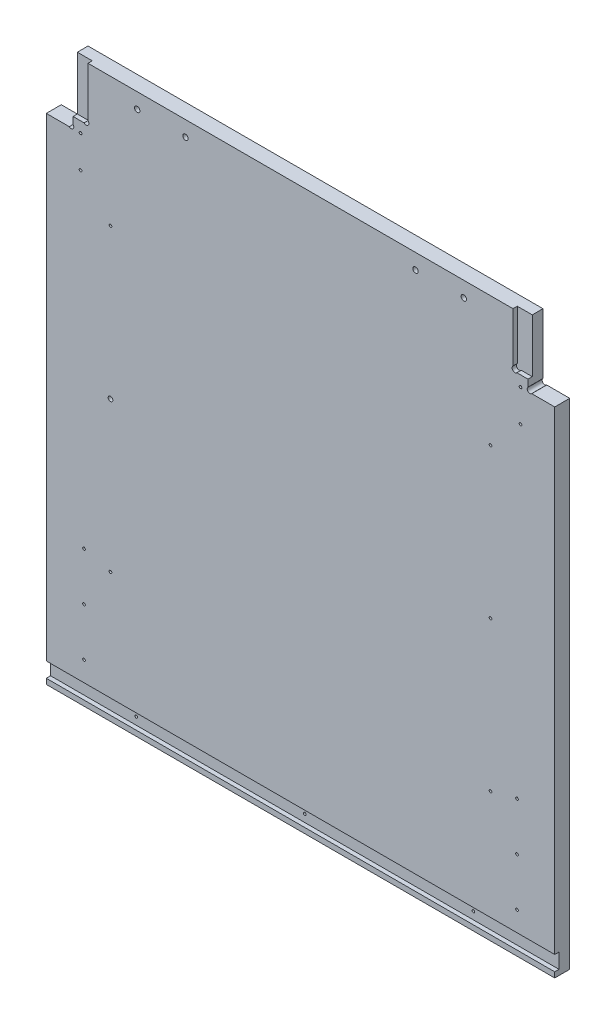
SolidWorks part; units mm, degrees
material "Pine"
ref_plane "Front Plane" through (0, 0, 0) normal (0, 0, 1) x (1, 0, 0)
ref_plane "Top Plane" through (0, 0, 0) normal (0, 1, 0) x (1, 0, 0)
ref_plane "Right Plane" through (0, 0, 0) normal (1, 0, 0) x (0, 0, -1)
sketch "Sketch1" plane through (0, 0, 0) normal (0, 0, 1) x (1, 0, 0)
  line L0 (8932.6508, -5243.5125) -> (10226.1458, -5243.5125)
  line L1 (9086.3208, -4722.0918) -> (10222.9708, -4853.7812)
  line L2 (8914.8708, -6342.0625) -> (10197.5708, -6342.0625)
  line L3 (8914.8708, -5808.6625) -> (10197.5708, -5808.6625)
  line L4 (8919.6333, -5253.0375) -> (10218.2083, -5253.0375)
  line L5 (9134.2633, -4656.1375) -> (9134.2633, -4638.3575)
  line L6 (9091.0833, -4638.3575) -> (9134.2633, -4638.3575)
  line L7 (9091.0833, -4567.2375) -> (9091.0833, -4638.3575)
  line L8 (9134.2633, -4656.1375) -> (9581.3033, -4656.1375)
  line L9 (9091.0833, -4567.2375) -> (9624.4833, -4567.2375)
  line L10 (9581.3033, -4656.1375) -> (9581.3033, -4638.3575)
  line L11 (9581.3033, -4638.3575) -> (9624.4833, -4638.3575)
  line L12 (9624.4833, -4567.2375) -> (9624.4833, -4638.3575)
  line L13 (8932.6508, -5225.7325) -> (9344.9775, -5225.7325)
  line L14 (8932.6508, -5256.2125) -> (8932.6508, -5243.5125)
  line L15 (8911.6958, -5256.2125) -> (8932.6508, -5256.2125)
  line L16 (8914.8708, -4722.0918) -> (9086.3208, -4722.0918)
  line L17 (8911.6958, -4715.5913) -> (8932.6508, -4715.5913)
  line L18 (8914.8708, -6342.0625) -> (8914.8708, -5808.6625)
  line L19 (12082.9917, -4722.0918) -> (10946.3417, -4853.7812)
  line L20 (12236.6617, -5243.5125) -> (10943.1667, -5243.5125)
  line L21 (10951.1042, -5253.0375) -> (12249.6792, -5253.0375)
  line L22 (10838.3917, -5656.2625) -> (11308.2917, -5656.2625)
  line L23 (10838.3917, -5719.7625) -> (11308.2917, -5719.7625)
  line L24 (10838.3917, -5742.5368) -> (11308.2917, -5742.5368)
  line L25 (10806.6417, -6342.0625) -> (11340.0417, -6342.0625)
  line L26 (10803.4667, -6335.7125) -> (11343.2167, -6335.7125)
  line L27 (10803.4667, -6317.9325) -> (11343.2167, -6317.9325)
  line L28 (10943.1667, -5225.7325) -> (11376.4483, -5225.7325)
  line L29 (11506.7292, -4754.5625) -> (10806.6417, -4827.5875)
  line L30 (11506.7292, -4567.2375) -> (11506.7292, -4754.5625)
  line L31 (10806.6417, -4567.2375) -> (10806.6417, -4827.5875)
  line L32 (10806.6417, -4567.2375) -> (11506.7292, -4567.2375)
  line L33 (10235.6708, -6329.3625) -> (10245.1958, -6329.3625)
  line L34 (10245.1958, -6329.3625) -> (10254.7208, -6278.5625)
  line L35 (10302.3458, -6329.3625) -> (10311.8708, -6278.5625)
  line L36 (10302.3458, -6329.3625) -> (10292.8208, -6329.3625)
  line L37 (10245.1958, -5821.3625) -> (10254.7208, -5872.1625)
  line L38 (10235.6708, -5821.3625) -> (10245.1958, -5821.3625)
  line L39 (10292.8208, -5821.3625) -> (10302.3458, -5821.3625)
  line L40 (10302.3458, -5821.3625) -> (10311.8708, -5872.1625)
  line L41 (10235.6708, -5821.3625) -> (10235.6708, -6329.3625)
  line L42 (10254.7208, -5872.1625) -> (10254.7208, -6278.5625)
  line L43 (10311.8708, -5872.1625) -> (10311.8708, -6278.5625)
  line L44 (10292.8208, -5821.3625) -> (10292.8208, -6329.3625)
  line L45 (8932.6508, -5225.7325) -> (8932.6508, -4715.5913)
  line L46 (8911.6958, -4715.5913) -> (8911.6958, -5256.2125)
  line L47 (8914.8708, -5248.275) -> (8914.8708, -4722.0918)
  line L48 (8919.6333, -5253.0375) -> (8914.8708, -5248.275)
  line L49 (8914.8708, -5145.0875) -> (8937.426, -5145.0875)
  line L50 (8914.8708, -5202.2375) -> (8937.426, -5202.2375)
  line L51 (10838.3917, -5656.2625) -> (10838.3917, -5719.7625)
  line L52 (10832.0417, -5736.1868) -> (10856.1717, -5736.1868)
  line L53 (10806.6417, -6342.0625) -> (10806.6417, -5818.7368)
  line L54 (10832.0417, -5649.9125) -> (10856.1717, -5649.9125)
  line L55 (10832.0417, -5726.1125) -> (10856.1717, -5726.1125)
  line L56 (10806.6417, -5818.7368) -> (10833.9015, -5818.7368)
  line L57 (10832.0417, -5806.0442) -> (10851.6815, -5806.0442)
  line L58 (10856.1717, -5801.5541) -> (10856.1717, -5736.1868)
  line L59 (10838.3917, -5814.2467) -> (10838.3917, -5742.5368)
  line L60 (10832.0417, -5806.0442) -> (10832.0417, -5736.1868)
  line L61 (10803.4667, -6317.9325) -> (10803.4667, -6335.7125)
  line L62 (10197.5708, -5808.6625) -> (10197.5708, -6342.0625)
  line L63 (9762.3842, -6348.4125) -> (9762.3842, -5802.3125)
  line L64 (9780.1642, -6348.4125) -> (9762.3842, -6348.4125)
  line L65 (9780.1642, -5802.3125) -> (9780.1642, -6348.4125)
  line L66 (9762.3842, -5802.3125) -> (9780.1642, -5802.3125)
  line L67 (9332.2775, -6348.4125) -> (9332.2775, -5802.3125)
  line L68 (9332.2775, -6348.4125) -> (9350.0575, -6348.4125)
  line L69 (9350.0575, -5802.3125) -> (9350.0575, -6348.4125)
  line L70 (9332.2775, -5802.3125) -> (9350.0575, -5802.3125)
  line L71 (9993.8374, -6061.075) -> (9993.8374, -6045.2418)
  line L72 (9998.5999, -6065.8375) -> (10014.4331, -6065.8375)
  line L73 (9998.5999, -6084.8875) -> (10014.4331, -6084.8875)
  line L74 (9993.8374, -6105.4832) -> (9993.8374, -6089.65)
  line L75 (9974.7874, -6105.4832) -> (9974.7874, -6089.65)
  line L76 (9954.1917, -6084.8875) -> (9970.0249, -6084.8875)
  line L77 (9974.7874, -6061.075) -> (9974.7874, -6045.2418)
  line L78 (9954.1917, -6065.8375) -> (9970.0249, -6065.8375)
  line L79 (10793.9417, -6237.2875) -> (10816.4969, -6237.2875)
  line L80 (10793.9417, -6294.4375) -> (10816.4969, -6294.4375)
  line L81 (10856.1717, -5649.9125) -> (10856.1717, -5726.1125)
  line L82 (10832.0417, -5726.1125) -> (10832.0417, -5649.9125)
  line L83 (10226.1458, -5225.7325) -> (10226.1458, -5243.5125)
  line L84 (10205.1908, -5257.8) -> (10205.1908, -4844.2499)
  line L85 (10230.9083, -4844.2499) -> (10230.9083, -5257.8)
  line L86 (10205.1908, -5257.8) -> (10230.9083, -5257.8)
  line L87 (10205.1908, -4844.2499) -> (10230.9083, -4844.2499)
  line L88 (10946.3417, -5176.8375) -> (10968.8969, -5176.8375)
  line L89 (9349.4676, -5141.9125) -> (9358.2674, -5141.9125)
  line L90 (10946.3417, -5119.6875) -> (10968.8969, -5119.6875)
  line L91 (9929.011, -4660.9635) -> (10066.0807, -4660.9635)
  line L92 (9929.011, -4678.7435) -> (10066.0807, -4678.7435)
  line L93 (10943.1667, -5225.7325) -> (10943.1667, -5243.5125)
  line L94 (10946.3417, -5248.275) -> (10951.1042, -5253.0375)
  line L95 (10946.3417, -5257.8063) -> (10946.3417, -4849.0188)
  line L96 (10964.1217, -5257.8) -> (10964.1217, -4844.2499)
  line L97 (10938.4042, -4844.2499) -> (10938.4042, -5257.8)
  line L98 (10938.4042, -5257.8) -> (10964.1217, -5257.8)
  line L99 (10964.1217, -4844.2499) -> (10938.4042, -4844.2499)
  line L100 (10344.8908, -4560.8875) -> (10369.0208, -4560.8875)
  line L101 (10344.8908, -4560.8875) -> (10369.0208, -4560.8875)
  line L102 (10800.2917, -4560.8875) -> (10824.4217, -4560.8875)
  line L103 (10200.4156, -5119.6875) -> (10222.9708, -5119.6875)
  line L104 (10200.4156, -5176.8375) -> (10222.9708, -5176.8375)
  line L105 (9344.9775, -5146.4026) -> (9344.9775, -5225.7325)
  line L106 (10344.8908, -4560.8875) -> (10344.8908, -4833.9375)
  line L107 (9792.8642, -5225.7325) -> (9792.8642, -5146.4026)
  line L108 (9362.7575, -5225.7325) -> (9775.0842, -5225.7325)
  line L109 (9680.3633, -4761.8396) -> (9680.3633, -4559.9604)
  line L110 (9656.2333, -4559.9604) -> (9680.3633, -4559.9604)
  line L111 (9656.2333, -4761.8396) -> (9680.3633, -4761.8396)
  line L112 (9656.2333, -4761.8396) -> (9656.2333, -4559.9604)
  line L113 (9779.5743, -5141.9125) -> (9788.374, -5141.9125)
  line L114 (10070.5708, -4665.4536) -> (10070.5708, -4674.2534)
  line L115 (9924.5208, -4674.2534) -> (9924.5208, -4665.4536)
  line L116 (12127.4417, -6188.3925) -> (12205.5015, -6188.3925)
  line L117 (12209.9917, -6170.6125) -> (12209.9917, -6183.9024)
  line L118 (9792.8642, -5225.7325) -> (10226.1458, -5225.7325)
  line L119 (9662.5833, -4754.5625) -> (10362.6708, -4827.5875)
  line L120 (9662.5833, -4567.2375) -> (9662.5833, -4754.5625)
  line L121 (10362.6708, -4567.2375) -> (10362.6708, -4827.5875)
  line L122 (9662.5833, -4567.2375) -> (10362.6708, -4567.2375)
  line L123 (10824.4217, -4833.9375) -> (10800.2917, -4833.9375)
  line L124 (10800.2917, -4833.9375) -> (10800.2917, -4560.8875)
  line L125 (10824.4217, -4560.8875) -> (10824.4217, -4833.9375)
  line L126 (10344.8908, -4833.9375) -> (10369.0208, -4833.9375)
  line L127 (10369.0208, -4833.9375) -> (10369.0208, -4560.8875)
  line L128 (10222.9708, -5248.275) -> (10218.2083, -5253.0375)
  line L129 (10222.9708, -5257.8063) -> (10222.9708, -4849.0188)
  line L130 (11734.6544, -5701.375) -> (11739.2301, -5701.375)
  line L131 (9362.7575, -5225.7325) -> (9362.7575, -5146.4026)
  line L132 (9775.0842, -5146.4026) -> (9775.0842, -5225.7325)
  line L133 (11761.3864, -5701.375) -> (11756.8282, -5701.375)
  line L134 (11734.6544, -5693.755) -> (11739.2301, -5693.755)
  line L135 (11761.4039, -5693.755) -> (11756.8282, -5693.755)
  line L136 (11734.6544, -5701.375) -> (11739.2301, -5701.375)
  line L137 (11744.3462, -5721.3024) -> (11744.3462, -5706.4179)
  line L138 (11751.7122, -5721.3024) -> (11751.7122, -5706.4179)
  line L139 (11740.0917, -6170.6125) -> (11740.0917, -6183.9024)
  line L140 (11689.2917, -6188.3925) -> (11822.6417, -6188.3925)
  line L141 (11689.2917, -6348.4093) -> (11689.2917, -6164.2657)
  line L142 (11689.2917, -6164.2657) -> (11746.4417, -6164.2657)
  line L143 (11746.4417, -6164.2657) -> (11746.4417, -6188.3925)
  line L144 (11689.2917, -6164.2657) -> (11746.4417, -6164.2657)
  line L145 (11340.0417, -5818.7368) -> (11340.0417, -6342.0625)
  line L146 (11290.5117, -5726.1125) -> (11314.6417, -5726.1125)
  line L147 (11290.5117, -5649.9125) -> (11290.5117, -5726.1125)
  line L148 (11340.0417, -5818.7368) -> (11312.7818, -5818.7368)
  line L149 (11314.6417, -5806.0442) -> (11295.0018, -5806.0442)
  line L150 (11290.5117, -5801.5541) -> (11290.5117, -5736.1868)
  line L151 (11308.2917, -5814.2467) -> (11308.2917, -5742.5368)
  line L152 (11314.6417, -5806.0442) -> (11314.6417, -5736.1868)
  line L153 (11290.5117, -5736.1868) -> (11314.6417, -5736.1868)
  line L154 (11848.0417, -6267.1325) -> (11962.3417, -6267.1325)
  line L155 (11962.3417, -6267.1325) -> (11962.3417, -6203.6325)
  line L156 (11343.2167, -6317.9325) -> (11343.2167, -6335.7125)
  line L157 (11365.4417, -5656.2625) -> (11365.4417, -5719.7625)
  line L158 (11365.4417, -5656.2625) -> (11479.7417, -5656.2625)
  line L159 (11778.1917, -6071.3937) -> (11802.3217, -6071.3937)
  line L160 (11314.6417, -5726.1125) -> (11314.6417, -5649.9125)
  line L161 (11314.6417, -5649.9125) -> (11290.5117, -5649.9125)
  line L162 (11308.2917, -5719.7625) -> (11308.2917, -5656.2625)
  line L163 (11689.2917, -6348.4093) -> (11713.4217, -6348.4093)
  line L164 (12203.6417, -6164.2657) -> (12260.7917, -6164.2657)
  line L165 (11713.4217, -6348.4093) -> (11713.4217, -6164.2657)
  line L166 (11695.6417, -6342.0625) -> (11695.6417, -6170.6125)
  line L167 (11695.6417, -6048.5337) -> (11699.4517, -6052.3437)
  line L168 (11822.6417, -6292.5325) -> (11822.6417, -6188.3925)
  line L169 (11695.6417, -6342.0625) -> (11695.6417, -6170.6125)
  line L170 (11848.0417, -6203.6325) -> (11962.3417, -6203.6325)
  line L171 (11848.0417, -6203.6325) -> (11848.0417, -6267.1325)
  line L172 (11987.7417, -6267.1325) -> (11987.7417, -6203.6325)
  line L173 (11784.5417, -6077.7437) -> (11784.5417, -6141.2438)
  line L174 (11517.8417, -5656.2625) -> (11632.1417, -5656.2625)
  line L175 (11632.1417, -5656.2625) -> (11632.1417, -5719.7625)
  line L176 (11632.1417, -5719.7625) -> (11517.8417, -5719.7625)
  line L177 (11517.8417, -5719.7625) -> (11517.8417, -5656.2625)
  line L178 (11692.4667, -6028.2137) -> (11692.4667, -6045.9937)
  line L179 (11695.6417, -5979.3188) -> (11718.1969, -5979.3188)
  line L180 (11695.6417, -5922.1687) -> (11718.1969, -5922.1687)
  line L181 (11821.0415, -5722.9375) -> (11821.0415, -5943.6)
  line L182 (11687.7042, -5651.5) -> (11701.9917, -5651.5)
  line L183 (11687.7042, -5651.5) -> (11687.7042, -6055.5251)
  line L184 (11687.7042, -6055.5251) -> (11701.9917, -6055.5251)
  line L185 (11701.9917, -6055.5251) -> (11701.9917, -5651.5)
  line L186 (11695.6417, -6055.2013) -> (11695.6417, -5649.595)
  line L187 (11695.6417, -5656.2625) -> (11695.6417, -6048.5337)
  line L188 (11695.6417, -6170.6125) -> (11740.0917, -6170.6125)
  line L189 (12203.6417, -6164.2657) -> (12203.6417, -6188.3925)
  line L190 (12254.4417, -6342.0625) -> (12254.4417, -6170.6125)
  line L191 (12129.0419, -5943.6) -> (12129.0419, -5722.9375)
  line L192 (12254.4417, -6048.5337) -> (12250.6317, -6052.3437)
  line L193 (12257.6167, -6045.9937) -> (12257.6167, -6028.2137)
  line L194 (12248.0917, -5651.5) -> (12262.3792, -5651.5)
  line L195 (12262.3792, -5651.5) -> (12262.3792, -6055.5251)
  line L196 (12262.3792, -6055.5251) -> (12248.0917, -6055.5251)
  line L197 (12248.0917, -6055.5251) -> (12248.0917, -5651.5)
  line L198 (12254.4417, -6141.2438) -> (12254.4417, -6077.7437)
  line L199 (12236.6617, -6164.2657) -> (12260.7917, -6164.2657)
  line L200 (12102.0417, -6267.1325) -> (11987.7417, -6267.1325)
  line L201 (11330.1865, -6237.2875) -> (11352.7417, -6237.2875)
  line L202 (11330.1865, -6294.4375) -> (11352.7417, -6294.4375)
  line L203 (11474.6617, -5851.8425) -> (11492.4417, -5851.8425)
  line L204 (11474.6617, -5808.6625) -> (11474.6617, -5851.8425)
  line L205 (11403.5417, -5808.6625) -> (11474.6617, -5808.6625)
  line L206 (11492.4417, -5851.8425) -> (11492.4417, -6298.8825)
  line L207 (11403.5417, -6342.0625) -> (11403.5417, -5808.6625)
  line L208 (11474.6617, -6298.8825) -> (11492.4417, -6298.8825)
  line L209 (11474.6617, -6342.0625) -> (11474.6617, -6298.8825)
  line L210 (11403.5417, -6342.0625) -> (11474.6617, -6342.0625)
  line L211 (11619.4417, -5851.8425) -> (11601.6617, -5851.8425)
  line L212 (11601.6617, -5808.6625) -> (11601.6617, -5851.8425)
  line L213 (11530.5417, -5808.6625) -> (11601.6617, -5808.6625)
  line L214 (11619.4417, -5851.8425) -> (11619.4417, -6298.8825)
  line L215 (11530.5417, -6342.0625) -> (11530.5417, -5808.6625)
  line L216 (11619.4417, -6298.8825) -> (11601.6617, -6298.8825)
  line L217 (11601.6617, -6342.0625) -> (11601.6617, -6298.8825)
  line L218 (11530.5417, -6342.0625) -> (11601.6617, -6342.0625)
  line L219 (11479.7417, -5719.7625) -> (11479.7417, -5656.2625)
  line L220 (11365.4417, -5719.7625) -> (11479.7417, -5719.7625)
  line L221 (11778.1917, -6147.5937) -> (11802.3217, -6147.5937)
  line L222 (11802.3217, -6071.3937) -> (11802.3217, -6147.5937)
  line L223 (11778.1917, -6147.5937) -> (11778.1917, -6071.3937)
  line L224 (12254.4417, -5922.1687) -> (12231.8865, -5922.1687)
  line L225 (12254.4417, -5979.3188) -> (12231.8865, -5979.3188)
  line L226 (12254.4417, -6055.2013) -> (12254.4417, -5649.595)
  line L227 (12254.4417, -6048.5337) -> (12254.4417, -5656.2625)
  line L228 (11841.6917, -5702.2873) -> (12108.3917, -5702.2873)
  line L229 (11822.6417, -6292.5325) -> (12127.4417, -6292.5325)
  line L230 (12127.4417, -6292.5325) -> (12127.4417, -6188.3925)
  line L231 (12254.4417, -6170.6125) -> (12209.9917, -6170.6125)
  line L232 (11695.6417, -6342.0625) -> (12254.4417, -6342.0625)
  line L233 (12236.6617, -6348.4093) -> (12260.7917, -6348.4093)
  line L234 (12260.7917, -6348.4093) -> (12260.7917, -6164.2657)
  line L235 (12236.6617, -6348.4093) -> (12236.6617, -6164.2657)
  line L236 (12102.0417, -6203.6325) -> (12102.0417, -6267.1325)
  line L237 (11987.7417, -6203.6325) -> (12102.0417, -6203.6325)
  line L238 (12236.6617, -6147.5937) -> (12236.6617, -6071.3937)
  line L239 (12203.6417, -6188.3925) -> (12260.7917, -6188.3925)
  line L240 (11098.7417, -4665.4536) -> (11098.7417, -4674.2534)
  line L241 (11394.2283, -5146.4026) -> (11394.2283, -5225.7325)
  line L242 (11376.4483, -5225.7325) -> (11376.4483, -5146.4026)
  line L243 (11394.2283, -5225.7325) -> (11806.555, -5225.7325)
  line L244 (11841.6917, -5964.2502) -> (12108.3917, -5964.2502)
  line L245 (12236.6617, -6147.5937) -> (12260.7917, -6147.5937)
  line L246 (12236.6617, -5256.2125) -> (12236.6617, -5243.5125)
  line L247 (12260.7917, -6147.5937) -> (12260.7917, -6071.3937)
  line L248 (12260.7917, -6071.3937) -> (12236.6617, -6071.3937)
  line L249 (12254.4417, -6077.7437) -> (11784.5417, -6077.7437)
  line L250 (11784.5417, -6141.2438) -> (12254.4417, -6141.2438)
  line L252 (12254.4417, -5656.2625) -> (11695.6417, -5656.2625)
  line L253 (11699.4517, -6052.3437) -> (12250.6317, -6052.3437)
  line L254 (11692.4667, -6045.9937) -> (12257.6167, -6045.9937)
  line L255 (11692.4667, -6028.2137) -> (12257.6167, -6028.2137)
  line L256 (11824.335, -5146.4026) -> (11824.335, -5225.7325)
  line L257 (11811.0451, -5141.9125) -> (11819.8449, -5141.9125)
  line L258 (11244.7917, -4674.2534) -> (11244.7917, -4665.4536)
  line L259 (11806.555, -5225.7325) -> (11806.555, -5146.4026)
  line L260 (11488.9492, -4761.8396) -> (11488.9492, -4559.9604)
  line L261 (11488.9492, -4559.9604) -> (11513.0792, -4559.9604)
  line L262 (11488.9492, -4761.8396) -> (11513.0792, -4761.8396)
  line L263 (11513.0792, -4761.8396) -> (11513.0792, -4559.9604)
  line L264 (11240.3015, -4660.9635) -> (11103.2318, -4660.9635)
  line L265 (11103.2318, -4678.7435) -> (11240.3015, -4678.7435)
  line L266 (12236.6617, -5225.7325) -> (12236.6617, -4715.5913)
  line L267 (12257.6167, -4715.5913) -> (12257.6167, -5256.2125)
  line L268 (12254.4417, -5248.275) -> (12254.4417, -4722.0918)
  line L269 (12236.6617, -5225.7325) -> (11824.335, -5225.7325)
  line L270 (12035.0492, -4656.1375) -> (12035.0492, -4638.3575)
  line L271 (12078.2292, -4638.3575) -> (12035.0492, -4638.3575)
  line L272 (12078.2292, -4567.2375) -> (12078.2292, -4638.3575)
  line L273 (12035.0492, -4656.1375) -> (11588.0092, -4656.1375)
  line L274 (11544.8292, -4567.2375) -> (12078.2292, -4567.2375)
  line L275 (11588.0092, -4656.1375) -> (11588.0092, -4638.3575)
  line L276 (11544.8292, -4638.3575) -> (11588.0092, -4638.3575)
  line L277 (11544.8292, -4567.2375) -> (11544.8292, -4638.3575)
  line L278 (12249.6792, -5253.0375) -> (12254.4417, -5248.275)
  line L280 (12257.6167, -5256.2125) -> (12236.6617, -5256.2125)
  line L281 (12231.8865, -5145.0875) -> (12254.4417, -5145.0875)
  line L282 (12231.8865, -5202.2375) -> (12254.4417, -5202.2375)
  line L283 (12236.6617, -4715.5913) -> (12257.6167, -4715.5913)
  line L284 (12082.9917, -4722.0918) -> (12254.4417, -4722.0918)
  line L285 (11380.9385, -5141.9125) -> (11389.7382, -5141.9125)
  circle A0 centre (8923.7608, -4778.9042) radius 1.5875
  circle A1 centre (9062.6598, -4736.3765) radius 2.3685
  circle A2 centre (9051.3958, -6281.7375) radius 22.225
  circle A3 centre (9083.1458, -6249.9875) radius 1.5875
  circle A4 centre (9083.1458, -6313.4875) radius 1.5875
  circle A5 centre (9019.6458, -6249.9875) radius 1.5875
  circle A6 centre (9019.6458, -6313.4875) radius 1.5875
  circle A7 centre (8972.3383, -5202.2375) radius 1.5875
  circle A8 centre (8923.7608, -5015.9708) radius 1.5875
  circle A9 centre (8923.7608, -5134.5042) radius 1.5875
  circle A10 centre (9054.5708, -5234.6225) radius 1.5875
  circle A11 centre (8923.7608, -4897.4375) radius 1.5875
  circle A12 centre (8972.3383, -5087.9375) radius 1.5875
  circle A13 centre (8972.3383, -5145.0875) radius 1.5875
  circle A14 centre (10847.2817, -5668.9625) radius 1.5875
  circle A15 centre (10847.2817, -5707.0625) radius 1.5875
  circle A16 centre (10847.2817, -5755.2368) radius 1.5875
  circle A17 centre (10851.4092, -6237.2875) radius 1.5875
  circle A18 centre (10851.4092, -6294.4375) radius 1.5875
  circle A19 centre (10847.2817, -5793.3442) radius 1.5875
  arc A20 (10833.9015, -5818.7368) -> (10838.3917, -5814.2467) centre (10836.1466, -5816.4918) ccw
  arc A21 (10851.6815, -5806.0442) -> (10856.1717, -5801.5541) centre (10853.9266, -5803.7992) ccw
  circle A22 centre (10882.8417, -6040.4375) radius 1.5875
  circle A23 centre (10882.8417, -6218.2375) radius 1.5875
  circle A24 centre (10882.8417, -5862.6375) radius 1.5875
  circle A25 centre (10908.2417, -6326.8225) radius 1.5875
  circle A26 centre (10908.2417, -6326.8225) radius 1.5875
  circle A27 centre (10851.4092, -6180.1375) radius 1.5875
  circle A28 centre (10815.5317, -4783.4231) radius 1.5875
  circle A29 centre (10815.5317, -4696.9488) radius 1.5875
  circle A30 centre (10815.5317, -4610.4746) radius 1.5875
  circle A31 centre (10979.1323, -4867.0082) radius 2.3685
  circle A32 centre (10190.1802, -4867.0082) radius 2.3685
  circle A33 centre (10955.2317, -4929.9812) radius 1.5875
  circle A34 centre (10955.2317, -5031.5812) radius 1.5875
  circle A35 centre (10214.0808, -4929.9812) radius 1.5875
  circle A36 centre (10214.0808, -5031.5812) radius 1.5875
  circle A37 centre (9341.1675, -6265.8625) radius 1.5875
  circle A38 centre (9771.2742, -5884.8625) radius 1.5875
  circle A39 centre (9771.2742, -6138.8625) radius 1.5875
  circle A40 centre (9771.2742, -6011.8625) radius 1.5875
  arc A41 (10036.2287, -6113.8083) -> (10051.3426, -6111.6033) centre (10042.9639, -6107.0732) ccw
  arc A42 (10051.3426, -6111.6033) -> (10051.3426, -6039.1217) centre (9984.3124, -6075.3625) ccw
  arc A43 (10051.3426, -6039.1217) -> (10036.2287, -6036.9167) centre (10042.9639, -6043.6518) ccw
  arc A44 (10034.5851, -6102.5431) -> (10034.5851, -6048.1819) centre (9984.3124, -6075.3625) ccw
  arc A45 (10034.5851, -6102.5431) -> (10036.2287, -6113.8083) centre (10042.9639, -6107.0732) ccw
  arc A46 (10036.2287, -6036.9167) -> (10034.5851, -6048.1819) centre (10042.9639, -6043.6518) ccw
  arc A47 (9945.8666, -6127.2787) -> (9948.0717, -6142.3927) centre (9952.6018, -6134.0139) ccw
  arc A48 (9948.0717, -6142.3927) -> (10020.5532, -6142.3927) centre (9984.3124, -6075.3625) ccw
  arc A49 (10020.5532, -6142.3927) -> (10022.7583, -6127.2787) centre (10016.0231, -6134.0139) ccw
  arc A50 (9957.1319, -6125.6352) -> (10011.493, -6125.6352) centre (9984.3124, -6075.3625) ccw
  arc A51 (9957.1319, -6125.6352) -> (9945.8666, -6127.2787) centre (9952.6018, -6134.0139) ccw
  arc A52 (10022.7583, -6127.2787) -> (10011.493, -6125.6352) centre (10016.0231, -6134.0139) ccw
  arc A53 (9932.3962, -6036.9167) -> (9917.2822, -6039.1217) centre (9925.661, -6043.6518) ccw
  arc A54 (9917.2822, -6039.1217) -> (9917.2822, -6111.6033) centre (9984.3124, -6075.3625) ccw
  arc A55 (9917.2822, -6111.6033) -> (9932.3962, -6113.8083) centre (9925.661, -6107.0732) ccw
  arc A56 (9934.0398, -6048.1819) -> (9934.0398, -6102.5431) centre (9984.3124, -6075.3625) ccw
  arc A57 (9934.0398, -6048.1819) -> (9932.3962, -6036.9167) centre (9925.661, -6043.6518) ccw
  arc A58 (9932.3962, -6113.8083) -> (9934.0398, -6102.5431) centre (9925.661, -6107.0732) ccw
  arc A59 (9945.8666, -6023.4463) -> (9957.1319, -6025.0898) centre (9952.6018, -6016.7111) ccw
  arc A60 (10011.493, -6025.0898) -> (10022.7583, -6023.4463) centre (10016.0231, -6016.7111) ccw
  arc A61 (10011.493, -6025.0898) -> (9957.1319, -6025.0898) centre (9984.3124, -6075.3625) ccw
  arc A62 (9948.0717, -6008.3323) -> (9945.8666, -6023.4463) centre (9952.6018, -6016.7111) ccw
  arc A63 (10020.5532, -6008.3323) -> (9948.0717, -6008.3323) centre (9984.3124, -6075.3625) ccw
  arc A64 (10022.7583, -6023.4463) -> (10020.5532, -6008.3323) centre (10016.0231, -6016.7111) ccw
  arc A65 (10005.0943, -6187.7574) -> (10096.7073, -6096.1443) centre (9984.3124, -6075.3625) ccw
  arc A66 (9993.8374, -6178.3911) -> (10005.0943, -6187.7574) centre (10003.3624, -6178.3911) ccw
  arc A67 (10001.6306, -6169.0249) -> (10077.9748, -6092.6807) centre (9984.3124, -6075.3625) ccw
  arc A68 (10087.3411, -6084.8875) -> (10077.9748, -6092.6807) centre (10087.3411, -6094.4125) ccw
  arc A69 (10001.6306, -6169.0249) -> (9993.8374, -6178.3911) centre (10003.3624, -6178.3911) ccw
  arc A70 (9963.5306, -6187.7574) -> (9974.7874, -6178.3911) centre (9965.2624, -6178.3911) ccw
  arc A71 (9871.9176, -6096.1443) -> (9963.5306, -6187.7574) centre (9984.3124, -6075.3625) ccw
  arc A72 (9881.2838, -6084.8875) -> (9871.9176, -6096.1443) centre (9881.2838, -6094.4125) ccw
  arc A73 (9890.65, -6092.6807) -> (9966.9943, -6169.0249) centre (9984.3124, -6075.3625) ccw
  arc A74 (9974.7874, -6178.3911) -> (9966.9943, -6169.0249) centre (9965.2624, -6178.3911) ccw
  arc A75 (9890.65, -6092.6807) -> (9881.2838, -6084.8875) centre (9881.2838, -6094.4125) ccw
  arc A76 (9871.9176, -6054.5807) -> (9881.2838, -6065.8375) centre (9881.2838, -6056.3125) ccw
  arc A77 (9963.5306, -5962.9676) -> (9871.9176, -6054.5807) centre (9984.3124, -6075.3625) ccw
  arc A78 (9974.7874, -5972.3339) -> (9963.5306, -5962.9676) centre (9965.2624, -5972.3339) ccw
  arc A79 (9966.9943, -5981.7001) -> (9890.65, -6058.0443) centre (9984.3124, -6075.3625) ccw
  arc A80 (9881.2838, -6065.8375) -> (9890.65, -6058.0443) centre (9881.2838, -6056.3125) ccw
  arc A81 (9966.9943, -5981.7001) -> (9974.7874, -5972.3339) centre (9965.2624, -5972.3339) ccw
  arc A82 (10077.9748, -6058.0443) -> (10087.3411, -6065.8375) centre (10087.3411, -6056.3125) ccw
  arc A83 (9993.8374, -5972.3339) -> (10001.6306, -5981.7001) centre (10003.3624, -5972.3339) ccw
  arc A84 (10077.9748, -6058.0443) -> (10001.6306, -5981.7001) centre (9984.3124, -6075.3625) ccw
  arc A85 (10087.3411, -6065.8375) -> (10096.7073, -6054.5807) centre (10087.3411, -6056.3125) ccw
  arc A86 (10096.7073, -6054.5807) -> (10005.0943, -5962.9676) centre (9984.3124, -6075.3625) ccw
  arc A87 (10005.0943, -5962.9676) -> (9993.8374, -5972.3339) centre (10003.3624, -5972.3339) ccw
  arc A88 (10014.4331, -6065.8375) -> (10018.7361, -6059.0339) centre (10014.4331, -6061.075) ccw
  arc A89 (10018.7361, -6059.0339) -> (10000.641, -6040.9388) centre (9984.3124, -6075.3625) ccw
  arc A90 (10000.641, -6040.9388) -> (9993.8374, -6045.2418) centre (9998.5999, -6045.2418) ccw
  arc A91 (9993.8374, -6061.075) -> (9998.5999, -6065.8375) centre (9998.5999, -6061.075) ccw
  arc A92 (9993.8374, -6105.4832) -> (10000.641, -6109.7862) centre (9998.5999, -6105.4832) ccw
  arc A93 (10000.641, -6109.7862) -> (10018.7361, -6091.6911) centre (9984.3124, -6075.3625) ccw
  arc A94 (10018.7361, -6091.6911) -> (10014.4331, -6084.8875) centre (10014.4331, -6089.65) ccw
  arc A95 (9998.5999, -6084.8875) -> (9993.8374, -6089.65) centre (9998.5999, -6089.65) ccw
  arc A96 (9954.1917, -6084.8875) -> (9949.8888, -6091.6911) centre (9954.1917, -6089.65) ccw
  arc A97 (9949.8888, -6091.6911) -> (9967.9839, -6109.7862) centre (9984.3124, -6075.3625) ccw
  arc A98 (9967.9839, -6109.7862) -> (9974.7874, -6105.4832) centre (9970.0249, -6105.4832) ccw
  arc A99 (9974.7874, -6089.65) -> (9970.0249, -6084.8875) centre (9970.0249, -6089.65) ccw
  arc A100 (9970.0249, -6065.8375) -> (9974.7874, -6061.075) centre (9970.0249, -6061.075) ccw
  arc A101 (9949.8888, -6059.0339) -> (9954.1917, -6065.8375) centre (9954.1917, -6061.075) ccw
  arc A102 (9967.9839, -6040.9388) -> (9949.8888, -6059.0339) centre (9984.3124, -6075.3625) ccw
  arc A103 (9974.7874, -6045.2418) -> (9967.9839, -6040.9388) centre (9970.0249, -6045.2418) ccw
  arc A104 (10096.7073, -6096.1443) -> (10087.3411, -6084.8875) centre (10087.3411, -6094.4125) ccw
  circle A105 centre (9771.2742, -6265.8625) radius 1.5875
  circle A106 centre (9341.1675, -5884.8625) radius 1.5875
  circle A107 centre (9341.1675, -6138.8625) radius 1.5875
  circle A108 centre (9341.1675, -6011.8625) radius 1.5875
  circle A109 centre (11037.2315, -4887.5494) radius 15.0812
  arc A110 (9349.4676, -5141.9125) -> (9344.9775, -5146.4026) centre (9347.2226, -5144.1576) ccw
  arc A111 (9362.7575, -5146.4026) -> (9358.2674, -5141.9125) centre (9360.5124, -5144.1576) ccw
  circle A112 centre (9946.7458, -4669.8535) radius 1.5875
  arc A113 (9924.5208, -4674.2534) -> (9929.011, -4678.7435) centre (9926.7659, -4676.4984) ccw
  circle A114 centre (11003.8092, -5176.8375) radius 1.5875
  circle A115 centre (11003.8092, -5119.6875) radius 1.5875
  circle A116 centre (10353.7808, -4696.9488) radius 1.5875
  circle A117 centre (10353.7808, -4610.4746) radius 1.5875
  circle A118 centre (10353.7808, -4783.4231) radius 1.5875
  circle A119 centre (11003.8092, -5062.5375) radius 1.5875
  circle A120 centre (9353.8675, -5160.9625) radius 1.5875
  circle A121 centre (9638.7708, -5234.6225) radius 1.5875
  circle A122 centre (9671.4733, -4724.1144) radius 1.5875
  circle A123 centre (9671.4733, -4661.3637) radius 1.5875
  circle A124 centre (9671.4733, -4598.6129) radius 1.5875
  arc A125 (9792.8642, -5146.4026) -> (9788.374, -5141.9125) centre (9790.6191, -5144.1576) ccw
  arc A126 (9779.5743, -5141.9125) -> (9775.0842, -5146.4026) centre (9777.3292, -5144.1576) ccw
  circle A127 centre (10048.3458, -4669.8535) radius 1.5875
  arc A128 (10070.5708, -4665.4536) -> (10066.0807, -4660.9635) centre (10068.3258, -4663.2086) ccw
  arc A129 (10066.0807, -4678.7435) -> (10070.5708, -4674.2534) centre (10068.3258, -4676.4984) ccw
  circle A130 centre (9997.5458, -4669.8535) radius 1.5875
  arc A131 (9929.011, -4660.9635) -> (9924.5208, -4665.4536) centre (9926.7659, -4663.2086) ccw
  circle A132 centre (10132.081, -4887.5494) radius 15.0812
  circle A133 centre (10165.5033, -5176.8375) radius 1.5875
  circle A134 centre (10165.5033, -5119.6875) radius 1.5875
  circle A135 centre (9486.3708, -5234.6225) radius 1.5875
  circle A136 centre (10165.5033, -5062.5375) radius 1.5875
  circle A137 centre (9206.9708, -5234.6225) radius 1.5875
  circle A138 centre (10070.5708, -5234.6225) radius 1.5875
  circle A139 centre (9918.1708, -5234.6225) radius 1.5875
  circle A140 centre (9783.9742, -5160.9625) radius 1.5875
  circle A141 centre (9783.9742, -5193.9825) radius 1.5875
  circle A142 centre (9353.8675, -5193.9825) radius 1.5875
  circle A143 centre (11073.3417, -6326.8225) radius 1.5875
  circle A144 centre (11073.3417, -6326.8225) radius 1.5875
  circle A145 centre (11295.2742, -6180.1375) radius 1.5875
  circle A146 centre (11295.2742, -6294.4375) radius 1.5875
  circle A147 centre (11295.2742, -6237.2875) radius 1.5875
  circle A148 centre (11975.0417, -5692.775) radius 3.4925
  circle A149 centre (11263.8417, -5862.6375) radius 1.5875
  arc A150 (11739.2301, -5701.375) -> (11744.3462, -5706.4179) centre (11748.0292, -5697.565) ccw
  arc A151 (11751.7122, -5706.4179) -> (11756.8282, -5701.375) centre (11748.0292, -5697.565) ccw
  arc A152 (11744.3462, -5721.3024) -> (11751.7122, -5721.3024) centre (11748.0292, -5725.505) ccw
  arc A153 (11734.6544, -5693.755) -> (11724.9787, -5697.565) centre (11730.5667, -5697.565) ccw
  arc A154 (11756.8282, -5693.755) -> (11739.2301, -5693.755) centre (11748.0292, -5697.565) ccw
  arc A155 (11724.9787, -5697.565) -> (11734.6544, -5701.375) centre (11730.5667, -5697.565) ccw
  arc A156 (11761.3864, -5701.375) -> (11771.0797, -5697.565) centre (11765.4842, -5697.565) ccw
  arc A157 (11771.0797, -5697.565) -> (11761.4039, -5693.755) centre (11765.4917, -5697.565) ccw
  arc A158 (11740.0917, -6183.9024) -> (11744.5818, -6188.3925) centre (11742.3367, -6186.1474) ccw
  arc A159 (12205.5015, -6188.3925) -> (12209.9917, -6183.9024) centre (12207.7466, -6186.1474) ccw
  circle A160 centre (11299.4017, -5793.3442) radius 1.5875
  arc A161 (11308.2917, -5814.2467) -> (11312.7818, -5818.7368) centre (11310.5367, -5816.4918) ccw
  arc A162 (11290.5117, -5801.5541) -> (11295.0018, -5806.0442) centre (11292.7567, -5803.7992) ccw
  circle A163 centre (11704.5317, -6314.149) radius 1.5875
  circle A164 centre (11748.9817, -6208.7125) radius 1.5875
  circle A165 centre (11263.8417, -6218.2375) radius 1.5875
  circle A166 centre (11263.8417, -6040.4375) radius 1.5875
  circle A167 centre (11238.4417, -6326.8225) radius 1.5875
  circle A168 centre (11238.4417, -6326.8225) radius 1.5875
  circle A169 centre (11299.4017, -5668.9625) radius 1.5875
  circle A170 centre (11299.4017, -5707.0625) radius 1.5875
  circle A171 centre (11726.7567, -6179.5025) radius 1.5875
  circle A172 centre (11704.5317, -6199.3198) radius 1.5875
  circle A173 centre (11748.9817, -6272.2125) radius 1.5875
  circle A174 centre (11704.5317, -6256.7344) radius 1.5875
  circle A175 centre (11299.4017, -5755.2368) radius 1.5875
  circle A176 centre (11913.4467, -6301.4225) radius 1.5875
  circle A177 centre (11790.2567, -6301.4225) radius 1.5875
  circle A178 centre (11793.4317, -6128.5437) radius 1.5875
  circle A179 centre (11753.1092, -5865.0188) radius 1.5875
  circle A180 centre (11809.9417, -6037.1038) radius 1.5875
  circle A181 centre (11809.9417, -6037.1038) radius 1.5875
  circle A182 centre (11753.1092, -5922.1687) radius 1.5875
  circle A183 centre (11975.0417, -5973.7625) radius 3.4925
  circle A184 centre (11975.0417, -6037.1038) radius 1.5875
  circle A185 centre (11753.1092, -5979.3188) radius 1.5875
  circle A186 centre (11975.0417, -6037.1038) radius 1.5875
  arc A187 (11841.6917, -5702.2873) -> (11821.0415, -5722.9375) centre (11841.6917, -5722.9375) ccw
  circle A188 centre (11811.5292, -5833.2687) radius 3.4925
  arc A189 (11821.0415, -5943.6) -> (11841.6917, -5964.2502) centre (11841.6917, -5943.6) ccw
  circle A190 centre (12196.9742, -5865.0188) radius 1.5875
  arc A191 (12129.0419, -5722.9375) -> (12108.3917, -5702.2873) centre (12108.3917, -5722.9375) ccw
  circle A192 centre (12036.6367, -6301.4225) radius 1.5875
  circle A193 centre (12159.8267, -6301.4225) radius 1.5875
  circle A194 centre (12138.5542, -5833.2687) radius 3.4925
  circle A195 centre (12197.2917, -5761.0375) radius 15.0812
  circle A196 centre (11793.4317, -6090.4437) radius 1.5875
  circle A197 centre (12196.9742, -5922.1687) radius 1.5875
  arc A198 (12108.3917, -5964.2502) -> (12129.0419, -5943.6) centre (12108.3917, -5943.6) ccw
  circle A199 centre (12196.9742, -5979.3188) radius 1.5875
  circle A200 centre (12201.1017, -6272.2125) radius 1.5875
  circle A201 centre (12245.5517, -6314.149) radius 1.5875
  circle A202 centre (12245.5517, -6256.7344) radius 1.5875
  circle A203 centre (12201.1017, -6208.7125) radius 1.5875
  circle A204 centre (12223.3267, -6179.5025) radius 1.5875
  circle A205 centre (12245.5517, -6199.3198) radius 1.5875
  circle A206 centre (11171.7667, -4669.8535) radius 1.5875
  circle A207 centre (11222.5667, -4669.8535) radius 1.5875
  arc A208 (11240.3015, -4678.7435) -> (11244.7917, -4674.2534) centre (11242.5466, -4676.4984) ccw
  circle A209 centre (11385.3383, -5193.9825) radius 1.5875
  circle A210 centre (12106.6527, -4736.3765) radius 2.3685
  circle A211 centre (12140.1417, -6037.1038) radius 1.5875
  circle A212 centre (12140.1417, -6037.1038) radius 1.5875
  circle A213 centre (12245.5517, -6090.4437) radius 1.5875
  circle A214 centre (12245.5517, -6128.5437) radius 1.5875
  circle A215 centre (11385.3383, -5160.9625) radius 1.5875
  arc A216 (11824.335, -5146.4026) -> (11819.8449, -5141.9125) centre (11822.0899, -5144.1576) ccw
  arc A217 (11811.0451, -5141.9125) -> (11806.555, -5146.4026) centre (11808.8001, -5144.1576) ccw
  circle A218 centre (11815.445, -5193.9825) radius 1.5875
  circle A219 centre (11815.445, -5160.9625) radius 1.5875
  circle A220 centre (11530.5417, -5234.6225) radius 1.5875
  circle A221 centre (11962.3417, -5234.6225) radius 1.5875
  arc A222 (11244.7917, -4665.4536) -> (11240.3015, -4660.9635) centre (11242.5466, -4663.2086) ccw
  circle A223 centre (11682.9417, -5234.6225) radius 1.5875
  circle A224 centre (11497.8392, -4724.1144) radius 1.5875
  circle A225 centre (11497.8392, -4661.3637) radius 1.5875
  circle A226 centre (11497.8392, -4598.6129) radius 1.5875
  circle A227 centre (11120.9667, -4669.8535) radius 1.5875
  arc A228 (11103.2318, -4660.9635) -> (11098.7417, -4665.4536) centre (11100.9867, -4663.2086) ccw
  arc A229 (11098.7417, -4674.2534) -> (11103.2318, -4678.7435) centre (11100.9867, -4676.4984) ccw
  circle A230 centre (12196.9742, -5202.2375) radius 1.5875
  circle A231 centre (12245.5517, -5015.9708) radius 1.5875
  circle A232 centre (12245.5517, -5134.5042) radius 1.5875
  circle A233 centre (12114.7417, -5234.6225) radius 1.5875
  circle A234 centre (12245.5517, -4897.4375) radius 1.5875
  circle A235 centre (12245.5517, -4778.9042) radius 1.5875
  circle A236 centre (12196.9742, -5087.9375) radius 1.5875
  circle A237 centre (12196.9742, -5145.0875) radius 1.5875
  circle A238 centre (11098.7417, -5234.6225) radius 1.5875
  circle A239 centre (11251.1417, -5234.6225) radius 1.5875
  arc A240 (11380.9385, -5141.9125) -> (11376.4483, -5146.4026) centre (11378.6934, -5144.1576) ccw
  arc A241 (11394.2283, -5146.4026) -> (11389.7382, -5141.9125) centre (11391.9833, -5144.1576) ccw
sketch "CabBack_Outline" plane through (0, 0, 0) normal (0, 0, 1) x (1, 0, 0)
  line L0 (10806.6417, -6342.0625) -> (11409.8917, -6342.0625)
  line L1 (11409.8917, -6342.0625) -> (11409.8917, -5755.3225)
  line L2 (11409.8917, -5755.3225) -> (11378.1417, -5755.3225)
  line L4 (11378.1417, -5755.3225) -> (11378.1417, -5679.1225)
  line L5 (10838.3917, -5679.1225) -> (10838.3917, -5755.3225)
  line L7 (10838.3917, -5755.3225) -> (10806.6417, -5755.3225)
  line L8 (10806.6417, -5755.3225) -> (10806.6417, -6342.0625)
  line L9 (10838.3917, -5679.1225) -> (11378.1417, -5679.1225)
  dimension "CabBack_Width" = 603.25
  dimension "Pedistal_EdgeGap" = 31.75
  dimension "PedistalHeight" = 76.2
  dimension "CabBack_Height" = 662.94
extrude "CabBack_Thickness" add sketch "CabBack_Outline" against normal blind 17.78
sketch "Sketch4" plane through (0, 0, 0) normal (0, 0, 1) x (1, 0, 0)
  line L0 (10838.3917, -5755.3225) -> (10836.1466, -5753.0774) construction
  line L1 (11378.1417, -5755.3225) -> (11380.3867, -5753.0774) construction
  line L2 (11409.8917, -5755.3225) -> (11378.1417, -5755.3225) construction
  line L3 (10838.3917, -5755.3225) -> (10806.6417, -5755.3225) construction
  circle A0 centre (11380.3867, -5753.0774) radius 3.175
  circle A1 centre (10836.1466, -5753.0774) radius 3.175
  dimension "D1" = 3.175
  dimension "D2" = 45
  dimension "D3" = 3.175
  dimension "D4" = 45
extrude "Cut-Extrude1" cut sketch "Sketch4" against normal up to surface (17.78 mm away) up to face at (11108.2667, -5882.9575, -17.78)
sketch "Sketch6" plane through (0, 0, 0) normal (0, 0, 1) x (1, 0, 0)
  line L0 (11108.2667, -6342.0625) -> (11108.2667, -6326.8225) construction
  line L1 (10806.6417, -6342.0625) -> (11409.8917, -6342.0625) construction
  line L2 (11108.2667, -6326.8225) -> (10908.2417, -6326.8225) construction
  line L3 (11108.2667, -6326.8225) -> (11308.2917, -6326.8225) construction
  line L4 (10847.2817, -5793.3442) -> (10847.2817, -5755.2368) construction
  line L5 (10847.2817, -5755.2368) -> (10847.2817, -5679.1225) construction
  line L6 (11378.1417, -5679.1225) -> (10838.3917, -5679.1225) construction
  line L7 (10847.2817, -5679.1225) -> (10838.3917, -5679.1225) construction
  line L8 (11369.2517, -5793.3442) -> (11369.2517, -5755.2368) construction
  line L9 (11369.2517, -5755.2368) -> (11369.2517, -5679.1225) construction
  line L10 (11369.2517, -5679.1225) -> (11378.1417, -5679.1225) construction
  line L11 (10806.6417, -6342.0625) -> (10806.6417, -5679.1225) construction
  line L12 (10806.6417, -6010.5925) -> (10882.8417, -6010.5925) construction
  line L13 (10882.8417, -5832.7925) -> (10882.8417, -6010.5925) construction
  line L14 (10806.6417, -5679.1225) -> (10838.3917, -5679.1225) construction
  line L15 (10882.8417, -6010.5925) -> (10882.8417, -6188.3925) construction
  line L16 (11409.8917, -6342.0625) -> (11409.8917, -5679.1225) construction
  line L17 (11409.8917, -5679.1225) -> (11378.1417, -5679.1225) construction
  line L18 (11409.8917, -6010.5925) -> (11333.6917, -6010.5925) construction
  line L19 (11333.6917, -5832.7925) -> (11333.6917, -6010.5925) construction
  line L20 (11333.6917, -6010.5925) -> (11333.6917, -6188.3925) construction
  line L21 (10851.4092, -6294.4375) -> (10851.4092, -6237.2875) construction
  line L22 (10851.4092, -6237.2875) -> (10851.4092, -6180.1375) construction
  line L23 (11365.1242, -6294.4375) -> (11365.1242, -6237.2875) construction
  line L24 (11365.1242, -6237.2875) -> (11365.1242, -6180.1375) construction
  circle A0 centre (10851.4092, -6294.4375) radius 1.5875
  circle A1 centre (10908.2417, -6326.8225) radius 1.5875
  circle A2 centre (11108.2667, -6326.8225) radius 1.5875
  circle A3 centre (11308.2917, -6326.8225) radius 1.5875
  circle A4 centre (11365.1242, -6294.4375) radius 1.5875
  circle A5 centre (11365.1242, -6237.2875) radius 1.5875
  circle A6 centre (11333.6917, -6188.3925) radius 1.5875
  circle A7 centre (11365.1242, -6180.1375) radius 1.5875
  circle A8 centre (11333.6917, -6010.5925) radius 1.5875
  circle A9 centre (11333.6917, -5832.7925) radius 1.5875
  circle A10 centre (11369.2517, -5793.3442) radius 1.5875
  circle A11 centre (11369.2517, -5755.2368) radius 1.5875
  circle A12 centre (10847.2817, -5755.2368) radius 1.5875
  circle A13 centre (10847.2817, -5793.3442) radius 1.5875
  circle A14 centre (10882.8417, -6010.5925) radius 2.7778
  circle A15 centre (10851.4092, -6180.1375) radius 1.5875
  circle A16 centre (10882.8417, -6188.3925) radius 1.5875
  circle A17 centre (10851.4092, -6237.2875) radius 1.5875
  circle A18 centre (10882.8417, -5832.7925) radius 1.5875
  dimension "D1" = 8.89
  dimension "D2" = 8.89
  dimension "D3" = 177.8
  dimension "D4" = 177.8
  dimension "D5" = 76.2
  dimension "D6" = 177.8
  dimension "D7" = 76.2
  dimension "D8" = 177.8
  dimension "D9" = 44.7675
  dimension "D10" = 104.775
  dimension "D11" = 44.7675
  dimension "D12" = 104.775
extrude "Cut-Extrude3" cut sketch "Sketch6" against normal up to surface (17.78 mm away) up to face at (11108.2667, -5856.9815, -17.78)
sketch "CabBack_LedgeCuts" plane through (0, 0, 0) normal (0, 0, 1) x (1, 0, 0)
  line L0 (11108.2667, -6317.9325) -> (11108.2667, -6342.0625) construction
  line L1 (10803.4667, -6317.9325) -> (11343.2167, -6317.9325) construction
  line L3 (11108.2667, -6317.9325) -> (10806.6417, -6317.9325)
  line L4 (10838.3917, -5679.1225) -> (10838.3917, -5742.6225)
  line L5 (11409.8917, -6342.0625) -> (11409.8917, -5755.3225) construction
  line L6 (11378.1417, -5679.1225) -> (11378.1417, -5742.6225)
  line L7 (10806.6417, -6342.0625) -> (11409.8917, -6342.0625) construction
  line L8 (10838.3917, -5742.6225) -> (10856.1717, -5742.6225)
  line L11 (11378.1417, -5742.6225) -> (11360.3617, -5742.6225)
  line L12 (10806.6417, -6342.0625) -> (10806.6417, -5818.7368) construction
  line L13 (10806.6417, -6317.9325) -> (10806.6417, -6335.7125)
  line L15 (10806.6417, -6335.7125) -> (11409.8917, -6335.7125)
  line L17 (10856.1717, -5742.6225) -> (10856.1717, -5679.1225)
  line L20 (10856.1717, -5679.1225) -> (10838.3917, -5679.1225)
  line L21 (11360.3617, -5742.6225) -> (11360.3617, -5679.1225)
  line L24 (11360.3617, -5679.1225) -> (11378.1417, -5679.1225)
  line L26 (11409.8917, -6317.9325) -> (11108.2667, -6317.9325)
  line L27 (11409.8917, -6335.7125) -> (11409.8917, -6317.9325)
  dimension "PedLedge_Thickness" = 17.78
  dimension "Pedistal_Thickness_2" = 17.78
  dimension "Bottom_Thickness" = 17.78
  dimension "Pedistal_Height" = 63.5
  dimension "Pedistal_Height_2" = 63.5
extrude "LedgeCuts_Depth" cut sketch "CabBack_LedgeCuts" against normal blind 5.08
sketch "Sketch7" plane through (0, 0, 0) normal (0, 0, 1) x (1, 0, 0)
  line L0 (10856.1717, -5742.6225) -> (10853.9266, -5740.3774) construction
  line L1 (11360.3617, -5742.6225) -> (11362.6067, -5740.3774) construction
  line L2 (10838.3917, -5742.6225) -> (10856.1717, -5742.6225) construction
  line L3 (11360.3617, -5742.6225) -> (11378.1417, -5742.6225) construction
  circle A0 centre (10853.9266, -5740.3774) radius 3.302
  circle A1 centre (11362.6067, -5740.3774) radius 3.302
  dimension "D1" = 45
  dimension "D2" = 3.175
  dimension "D3" = 45
  dimension "D4" = 3.175
extrude "Cut-Extrude4" cut sketch "Sketch7" against normal up to surface (5.08 mm away) up to face at (10847.2817, -5710.8725, -5.08)
sketch "Sketch9" plane through (0, 0, 0) normal (0, 0, 1) x (1, 0, 0)
  circle A0 centre (10914.5417, -5697.23) radius 3.175
  circle A1 centre (10971.7417, -5697.23) radius 3.175
  circle A2 centre (11244.7417, -5697.23) radius 3.175
  circle A3 centre (11301.9417, -5697.23) radius 3.175
extrude "Cut-Extrude5" cut sketch "Sketch9" against normal up to surface (17.78 mm away) up to face at (10884.4292, -5832.7925, -17.78)
